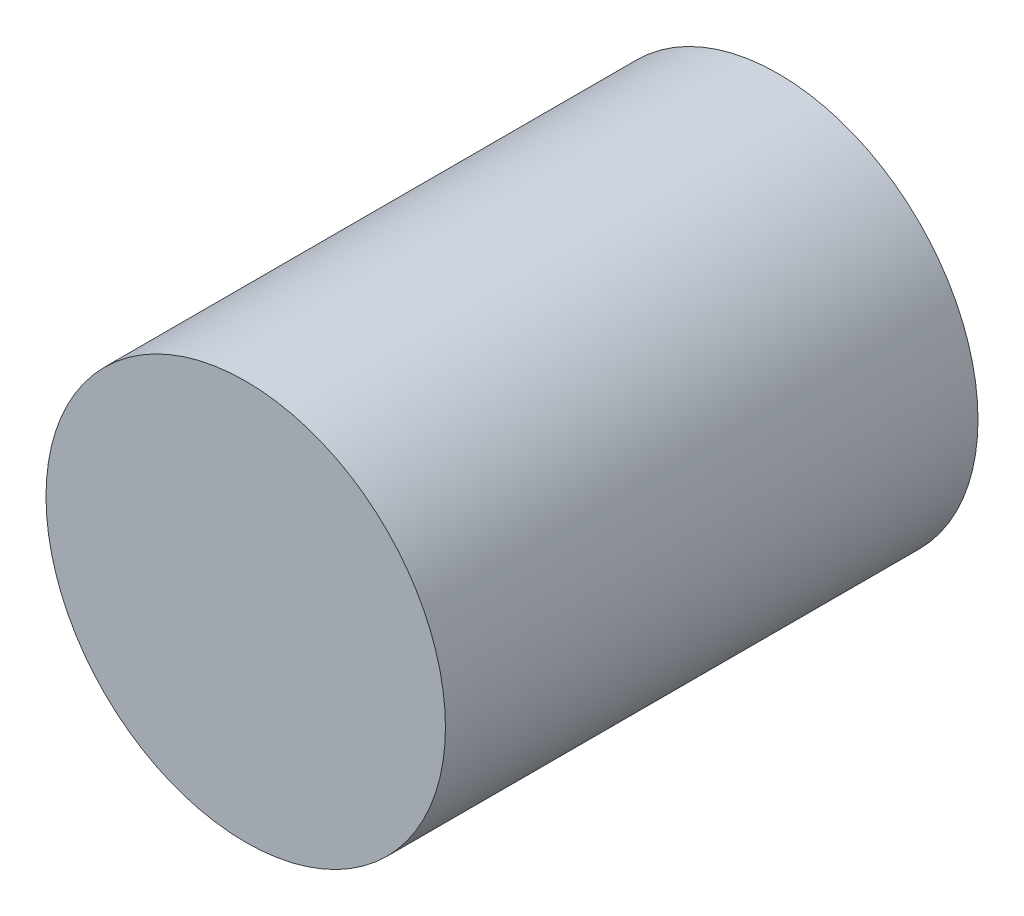
SolidWorks part; units mm, degrees
material "Alloy Steel"
ref_plane "Front Plane" through (0, 0, 0) normal (0, 0, 1) x (1, 0, 0)
ref_plane "Top Plane" through (0, 0, 0) normal (0, 1, 0) x (1, 0, 0)
ref_plane "Right Plane" through (0, 0, 0) normal (1, 0, 0) x (0, 0, -1)
sketch "Sketch2" plane through (0, 0, 0) normal (0, 0, 1) x (1, 0, 0)
  circle A0 centre (0, 0) radius 4.7625
  dimension "D1" = 9.525
extrude "Boss-Extrude1" add sketch "Sketch2" along normal blind 12.7
